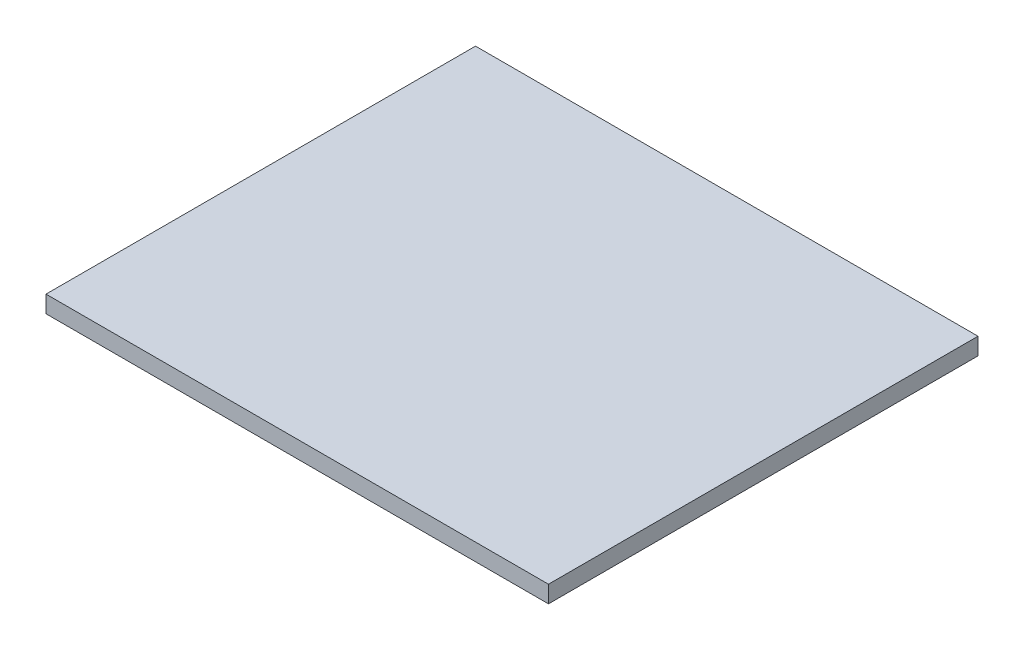
SolidWorks part; units mm, degrees
ref_plane "Front Plane" through (0, 0, 0) normal (0, 0, 1) x (1, 0, 0)
ref_plane "Top Plane" through (0, 0, 0) normal (0, 1, 0) x (1, 0, 0)
ref_plane "Right Plane" through (0, 0, 0) normal (1, 0, 0) x (0, 0, -1)
sketch "Sketch1" plane through (0, 0, 0) normal (0, 1, 0) x (1, 0, 0)
  line L0 (310, -265) -> (310, 239.3548)
  line L1 (310, 239.3548) -> (-280, 239.3548)
  line L3 (310, -265) -> (-280, -265)
  line L4 (-280, 239.3548) -> (-280, -265)
  point P0 (0, 0)
  point P6 (252.9032, 239.3548)
  point P8 (300.7477, 239.3548)
  dimension "D1" = 590
extrude "Boss-Extrude1" add sketch "Sketch1" along normal blind 20
